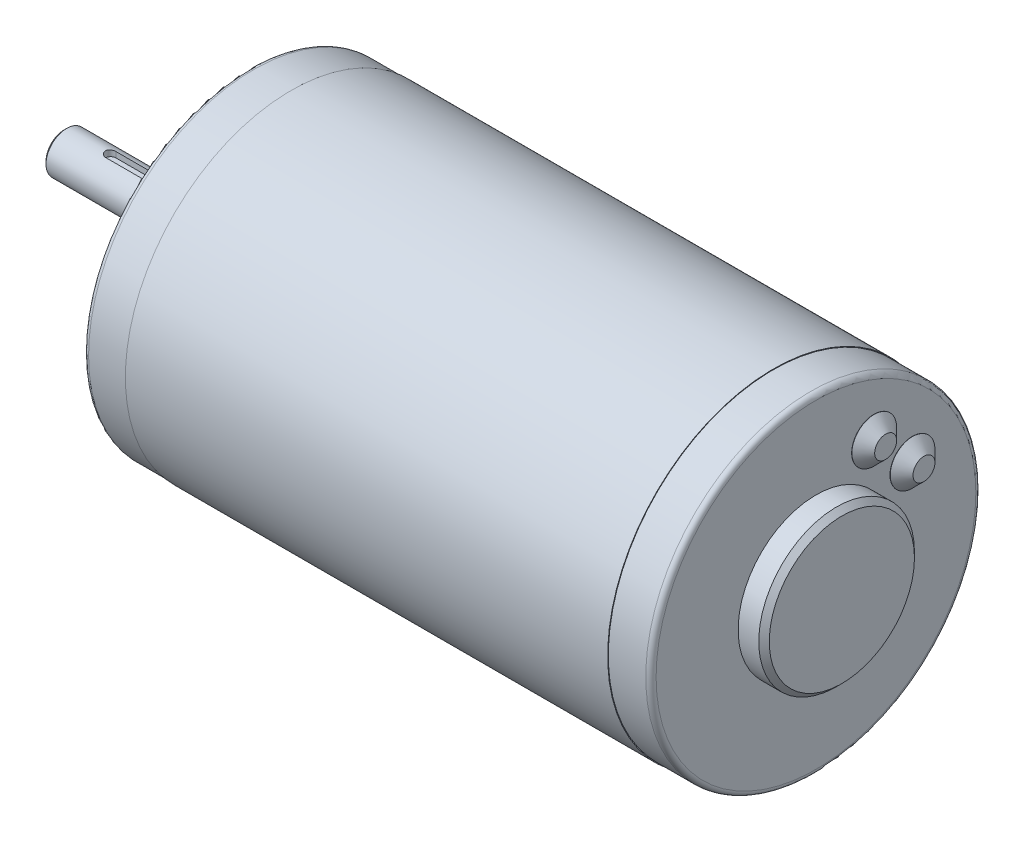
SolidWorks part; units mm, degrees
ref_plane "Front Plane" through (0, 0, 0) normal (0, 0, 1) x (1, 0, 0)
ref_plane "Top Plane" through (0, 0, 0) normal (0, 1, 0) x (1, 0, 0)
ref_plane "Right Plane" through (0, 0, 0) normal (1, 0, 0) x (0, 0, -1)
sketch "Sketch1" plane through (0, 0, 0) normal (0, 0, 1) x (1, 0, 0)
  line L0 (8.2296, 32.004) -> (8.2296, 0)
  line L1 (8.2296, 0) -> (101.3704, 0)
  line L2 (101.3704, 0) -> (101.3704, 32.004)
  line L3 (101.3704, 32.004) -> (8.2296, 32.004)
  line L4 (8.2296, 0) -> (101.3704, 0) construction
revolve "Revolve1" add sketch "Sketch1" angle 360 about L4
sketch "Sketch2" plane through (101.3704, 0, 0) normal (1, 0, 0) x (0, 0, -1)
  circle A0 centre (0, 0) radius 31.877
extrude "Boss-Extrude1" add sketch "Sketch2" along normal blind 8.2296
sketch "Sketch3" plane through (109.6, 0, 0) normal (1, 0, 0) x (0, 0, -1)
  circle A0 centre (0, 0) radius 15.0368
extrude "Boss-Extrude2" add sketch "Sketch3" along normal blind 3.984
sketch "Sketch4" plane through (113.584, 0, 0) normal (1, 0, 0) x (0, 0, -1)
  circle A0 centre (0, 0) radius 15.0368
extrude "Boss-Extrude3" add sketch "Sketch4" along normal blind 1.016 draft 45
sketch "Sketch5" plane through (8.2296, 0, 0) normal (-1, 0, 0) x (0, 0, 1)
  circle A0 centre (0, 0) radius 31.877
extrude "Boss-Extrude4" add sketch "Sketch5" along normal blind 8.2296
sketch "Sketch6" plane through (0, 0, 0) normal (-1, 0, 0) x (0, 0, 1)
  circle A0 centre (0, 0) radius 9.525
extrude "Boss-Extrude5" add sketch "Sketch6" along normal blind 4
sketch "Sketch7" plane through (-4, 0, 0) normal (-1, 0, 0) x (0, 0, 1)
  circle A0 centre (0, 0) radius 4
extrude "Boss-Extrude6" add sketch "Sketch7" along normal blind 31.6
ref_plane "Plane1" through (0, 2.8, 0) normal (0, -1, 0) x (1, 0, 0)
sketch "Sketch8" plane through (0, 2.8, 0) normal (0, -1, 0) x (1, 0, 0)
  line L0 (-7.1, 1) -> (-26.6, 1)
  line L1 (-26.6, -1) -> (-7.1, -1)
  arc A0 (-7.1, -1) -> (-7.1, 1) centre (-7.1, 0) ccw
  arc A1 (-26.6, 1) -> (-26.6, -1) centre (-26.6, 0) ccw
ref_plane "Plane2" through (0, 0, -18.6071) normal (0, 0, 1) x (1, 0, 0)
sketch "Sketch9" plane through (0, 0, -18.6071) normal (0, 0, 1) x (1, 0, 0)
  line L0 (109.6, 15.5254) -> (109.6, 11.2074)
  line L1 (109.6, 11.2074) -> (111.8479, 11.2074)
  line L2 (111.8479, 11.2074) -> (111.8479, 13.3254)
  line L3 (111.8479, 13.3254) -> (109.6479, 15.5254)
  line L4 (109.6479, 15.5254) -> (109.6, 15.5254)
  line L5 (109.6, 11.2074) -> (111.8479, 11.2074) construction
revolve "Revolve2" add sketch "Sketch9" angle 360 about L5
ref_plane "Plane3" through (0, 0, -11.2074) normal (0, 0, 1) x (1, 0, 0)
sketch "Sketch10" plane through (0, 0, -11.2074) normal (0, 0, 1) x (1, 0, 0)
  line L0 (109.6, 22.9251) -> (109.6, 18.6071)
  line L1 (109.6, 18.6071) -> (111.8479, 18.6071)
  line L2 (111.8479, 18.6071) -> (111.8479, 20.7251)
  line L3 (111.8479, 20.7251) -> (109.6479, 22.9251)
  line L4 (109.6479, 22.9251) -> (109.6, 22.9251)
  line L5 (109.6, 18.6071) -> (111.8479, 18.6071) construction
revolve "Revolve3" add sketch "Sketch10" angle 360 about L5
hole_wizard "M3.5 Clearance Hole1" positions "Sketch12" profile "Sketch11" hole size "M3.5" standard "ANSI Metric"
sketch "Sketch12" plane through (0, 0, 0) normal (-1, 0, 0) x (0, 0, 1)
  point P0 (0, 25.4)
  point P1 (0, -25.4)
sketch "Sketch11" plane through (0, 25.4, 0) normal (0, 1, 0) x (0, 0, 1)
  line L0 (0, 0) -> (0, 14.8277)
  line L1 (0, 14.8277) -> (2.0193, 13.6144)
  line L2 (2.0193, 13.6144) -> (2.0193, 0)
  line L5 (2.0193, 0) -> (0, 0)
  line L10 (0, 14.8277) -> (-2.0193, 13.6144) construction
  line L11 (0, -6.35) -> (0, 107.95) construction
  dimension "Hole Dia." = 4.0386
  dimension "Hole Depth" = 13.6144
  dimension "Drill Angle" = 118
chamfer "Chamfer1" distance 1.016 angle 45 1 edges at (-4, 0, 9.525)
chamfer "Chamfer2" distance 0.5 angle 45 1 edges at (-35.6, 0, 4)
fillet "Fillet1" radius 1 2 edges at (109.6, 0, -31.877) (0, 0, 31.877)
extrude "Cut-Extrude2" cut sketch "Sketch8" against normal blind 2.54 contours A0 L0 A1 L1
